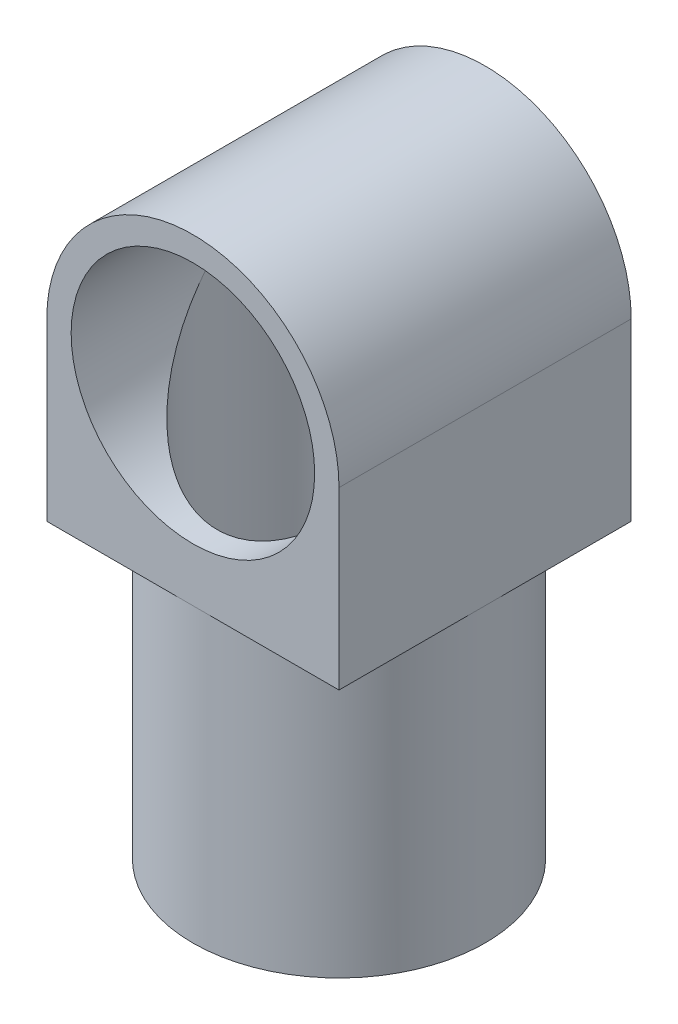
SolidWorks part; units mm, degrees
material "6061-T6 (SS)"
ref_plane "Front Plane" through (0, 0, 0) normal (0, 0, 1) x (1, 0, 0)
ref_plane "Top Plane" through (0, 0, 0) normal (0, 1, 0) x (1, 0, 0)
ref_plane "Right Plane" through (0, 0, 0) normal (1, 0, 0) x (0, 0, -1)
sketch "Sketch1" plane through (0, 0, 0) normal (0, 0, 1) x (1, 0, 0)
  line L0 (-15, 0) -> (-15, -15)
  line L1 (-15, -15) -> (-15, -18)
  line L2 (-15, -18) -> (15, -18)
  line L3 (15, -18) -> (15, 0)
  circle A0 centre (0, 0) radius 12.5
  circle A1 centre (0, 0) radius 15
  dimension "D1" = 25
  dimension "D2" = 30
  dimension "D3" = 3
  dimension "D4" = 15
extrude "Boss-Extrude2" add sketch "Sketch1" along normal blind 30 contours A1 L0 L1 L2 L3 | A1 A0
sketch "Sketch3" plane through (0, -18, 0) normal (0, -1, 0) x (1, 0, 0)
  line L0 (-15, 15) -> (15, 15) construction
  line L1 (-15, 30) -> (-15, 0) construction
  line L2 (15, 30) -> (15, 0) construction
  line L3 (0, 0) -> (0, 30) construction
  line L4 (-15, 30) -> (15, 30) construction
  circle A0 centre (0, 15) radius 12.5
  circle A1 centre (0, 15) radius 15
  dimension "D1" = 25
extrude "Boss-Extrude3" add sketch "Sketch3" along normal blind 30
sketch "Sketch4" plane through (0, -18, 0) normal (0, -1, 0) x (1, 0, 0)
  line L0 (0, 0) -> (0, 30) construction
  line L1 (-15, 15) -> (15, 15) construction
  circle A0 centre (0, 15) radius 12.5
  circle A1 centre (0, 15) radius 15 construction
  dimension "D1" = 25
extrude "Cut-Extrude1" cut sketch "Sketch4" against normal blind 18
